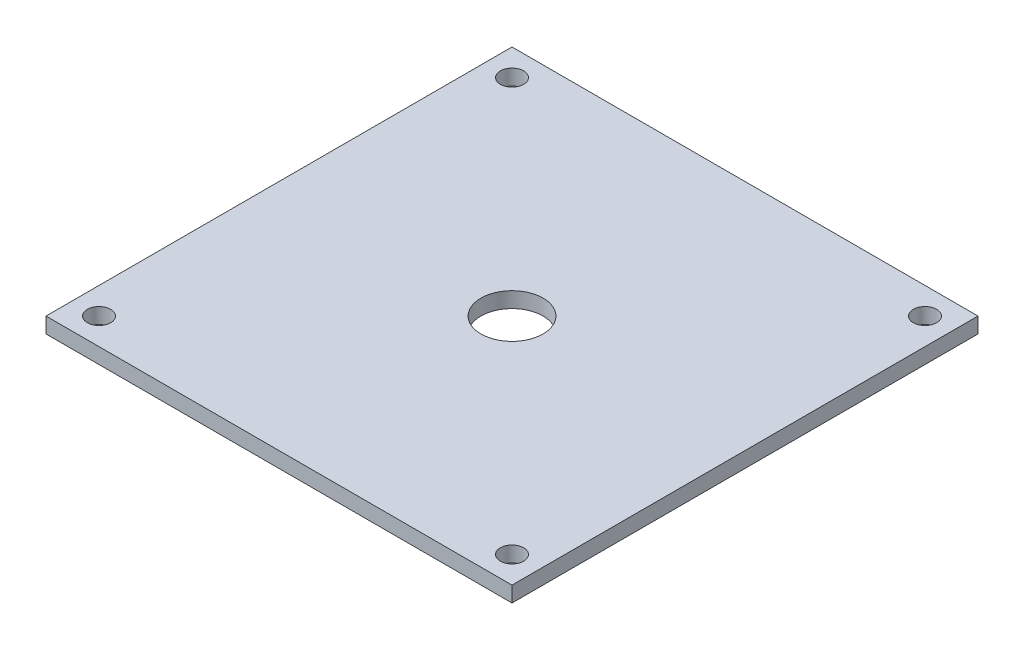
SolidWorks part; units mm, degrees
ref_plane "Alzado" through (0, 0, 0) normal (0, 0, 1) x (1, 0, 0)
ref_plane "Planta" through (0, 0, 0) normal (0, 1, 0) x (1, 0, 0)
ref_plane "Vista lateral" through (0, 0, 0) normal (1, 0, 0) x (0, 0, -1)
sketch "Croquis1" plane through (0, 0, 0) normal (0, 1, 0) x (1, 0, 0)
  line L1 (-150, -150) -> (150, -150)
  line L2 (-150, -150) -> (-150, 150)
  line L3 (-150, 150) -> (150, 150)
  line L4 (150, -150) -> (150, 150)
  line L5 (-150, -150) -> (150, 150) construction
  line L6 (-150, 150) -> (150, -150) construction
  circle A0 centre (0, 0) radius 20
  circle A1 centre (0, 0) radius 188 construction
  circle A2 centre (-132.9361, 132.9361) radius 7.5
  circle A3 centre (132.9361, 132.9361) radius 7.5
  circle A4 centre (132.9361, -132.9361) radius 7.5
  circle A5 centre (-132.9361, -132.9361) radius 7.5
  point P0 (0, 0)
  point P20 (0, 0)
  dimension "D1" = 300
  dimension "D2" = 40
  dimension "D3" = 376
  dimension "D4" = 15
  dimension "D5" = 4
extrude "Saliente-Extruir1" add sketch "Croquis1" along normal blind 10
